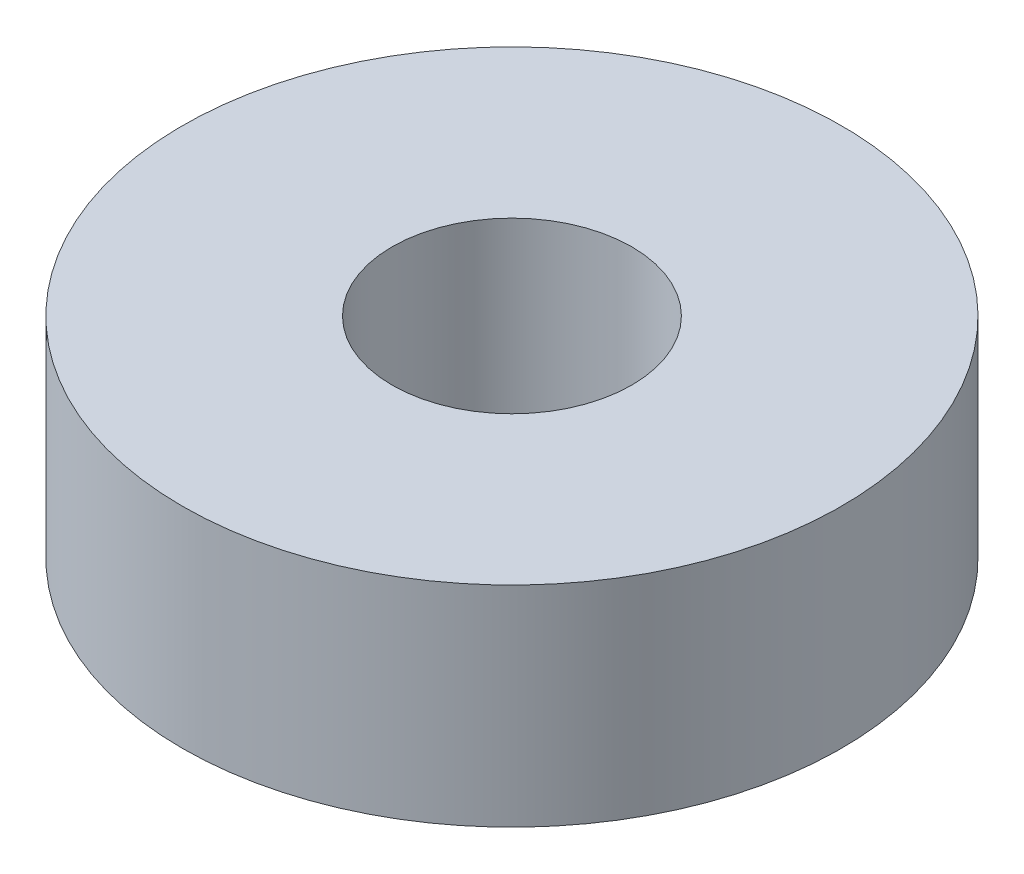
SolidWorks part; units mm, degrees
ref_plane "Front Plane" through (0, 0, 0) normal (0, 0, 1) x (1, 0, 0)
ref_plane "Top Plane" through (0, 0, 0) normal (0, 1, 0) x (1, 0, 0)
ref_plane "Right Plane" through (0, 0, 0) normal (1, 0, 0) x (0, 0, -1)
sketch "Sketch5" plane through (0, 0, 0) normal (0, 1, 0) x (1, 0, 0)
  circle A0 centre (0, 0) radius 11
  dimension "D1" = 22
extrude "Boss-Extrude2" add sketch "Sketch5" along normal blind 7
sketch "Sketch6" plane through (0, 7, 0) normal (0, 1, 0) x (1, 0, 0)
  circle A0 centre (0, 0) radius 4
  dimension "D1" = 8
extrude "Cut-Extrude3" cut sketch "Sketch6" against normal blind 8
